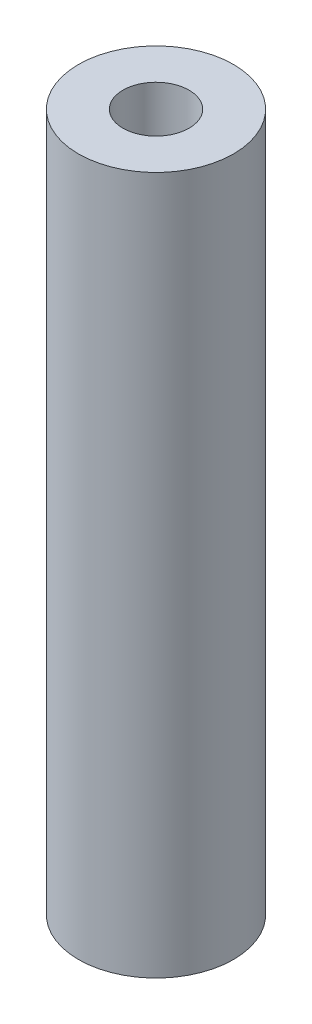
SolidWorks part; units mm, degrees
ref_plane "Front Plane" through (0, 0, 0) normal (0, 0, 1) x (1, 0, 0)
ref_plane "Top Plane" through (0, 0, 0) normal (0, 1, 0) x (1, 0, 0)
ref_plane "Right Plane" through (0, 0, 0) normal (1, 0, 0) x (0, 0, -1)
sketch "Sketch1" plane through (0, 0, 0) normal (0, 1, 0) x (1, 0, 0)
  circle A0 centre (0, 0) radius 3.175
  dimension "D1" = 6.35
extrude "Boss-Extrude1" add sketch "Sketch1" along normal blind 28.575
hole_wizard "Tap Drill for #6-32 Tap1" positions "Sketch3" profile "Sketch2" hole size "#6-32" standard "ANSI Inch" end condition through all
sketch "Sketch3" plane through (0, 28.575, 0) normal (0, 1, 0) x (1, 0, 0)
  point P0 (0, 0)
sketch "Sketch2" plane through (0, 28.575, 0) normal (1, 0, 0) x (0, 0, 1)
  line L0 (0, 0) -> (0, 28.575)
  line L1 (0, 28.575) -> (1.3525, 28.575)
  line L2 (1.3525, 28.575) -> (1.3525, 0)
  line L5 (1.3525, 0) -> (0, 0)
  line L11 (0, -6.35) -> (0, 107.95) construction
  dimension "Thru Hole Dia." = 2.7051
  dimension "Thru Hole Depth" = 28.575
